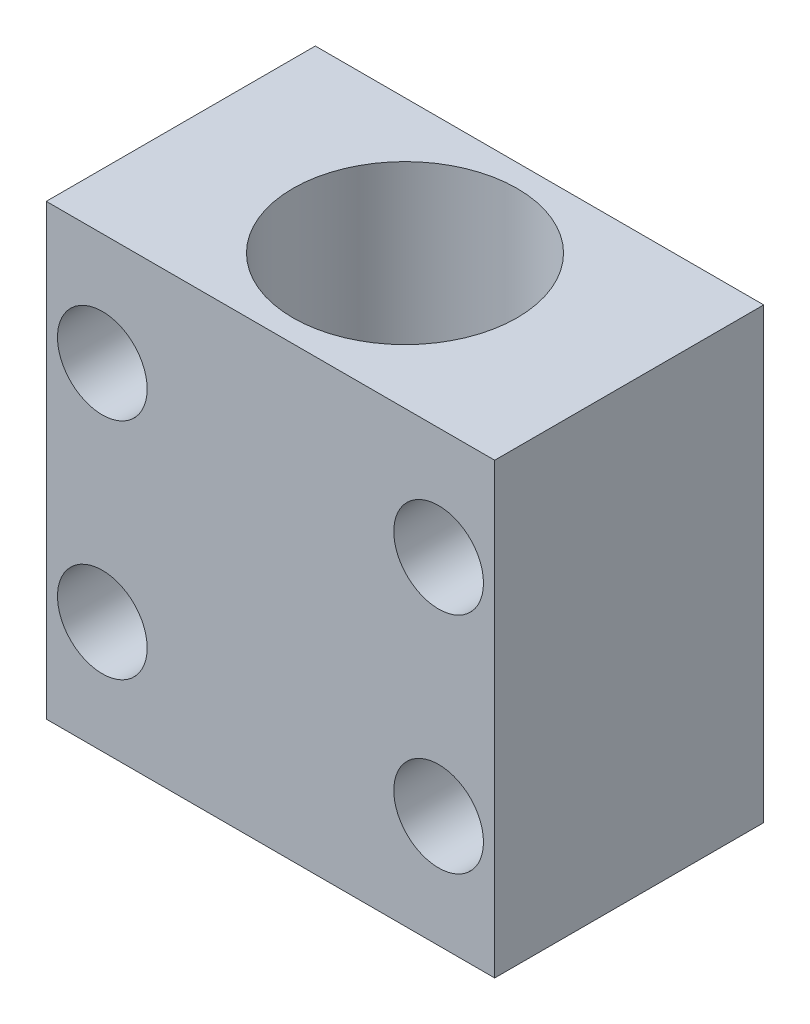
SolidWorks part; units mm, degrees
ref_plane "Front Plane" through (0, 0, 0) normal (0, 0, 1) x (1, 0, 0)
ref_plane "Top Plane" through (0, 0, 0) normal (0, 1, 0) x (1, 0, 0)
ref_plane "Right Plane" through (0, 0, 0) normal (1, 0, 0) x (0, 0, -1)
sketch "Sketch2" plane through (0, 0, 0) normal (0, 1, 0) x (1, 0, 0)
  line L1 (-63.5, 38.1) -> (63.5, 38.1)
  line L2 (-63.5, 38.1) -> (-63.5, -38.1)
  line L3 (-63.5, -38.1) -> (63.5, -38.1)
  line L4 (63.5, 38.1) -> (63.5, -38.1)
  line L5 (-63.5, 38.1) -> (63.5, -38.1) construction
  line L6 (-63.5, -38.1) -> (63.5, 38.1) construction
  circle A0 centre (0, 0) radius 31.75
  dimension "D1" = 63.5
  dimension "D2" = 76.2
  dimension "D3" = 127
extrude "Boss-Extrude1" add sketch "Sketch2" along normal blind 127
sketch "Sketch3" plane through (0, 0, 38.1) normal (0, 0, 1) x (1, 0, 0)
  line L0 (63.5, 127) -> (31.75, 127)
  line L1 (47.625, 127) -> (47.625, 0)
  line L2 (-63.5, 0) -> (63.5, 0) construction
  line L3 (-31.75, 127) -> (-63.5, 127)
  line L4 (-47.625, 127) -> (-47.625, 0)
  line L5 (-47.625, 127) -> (-47.625, 63.5)
  line L6 (-47.625, 63.5) -> (-47.625, 0)
  line L7 (-47.625, 127) -> (-47.625, 63.5)
  circle A0 centre (-47.625, 31.75) radius 12.7
  circle A1 centre (47.625, 31.75) radius 12.7
  circle A2 centre (-47.625, 95.25) radius 12.7
  circle A3 centre (47.625, 95.25) radius 12.7
  dimension "D1" = 25.4
  dimension "D2" = 25.4
  dimension "D3" = 25.4
  dimension "D4" = 25.4
extrude "Cut-Extrude1" cut sketch "Sketch3" against normal blind 127 contours L1 A3 | L1 A3 | L1 A1 | L1 A1 | A0 | A2
